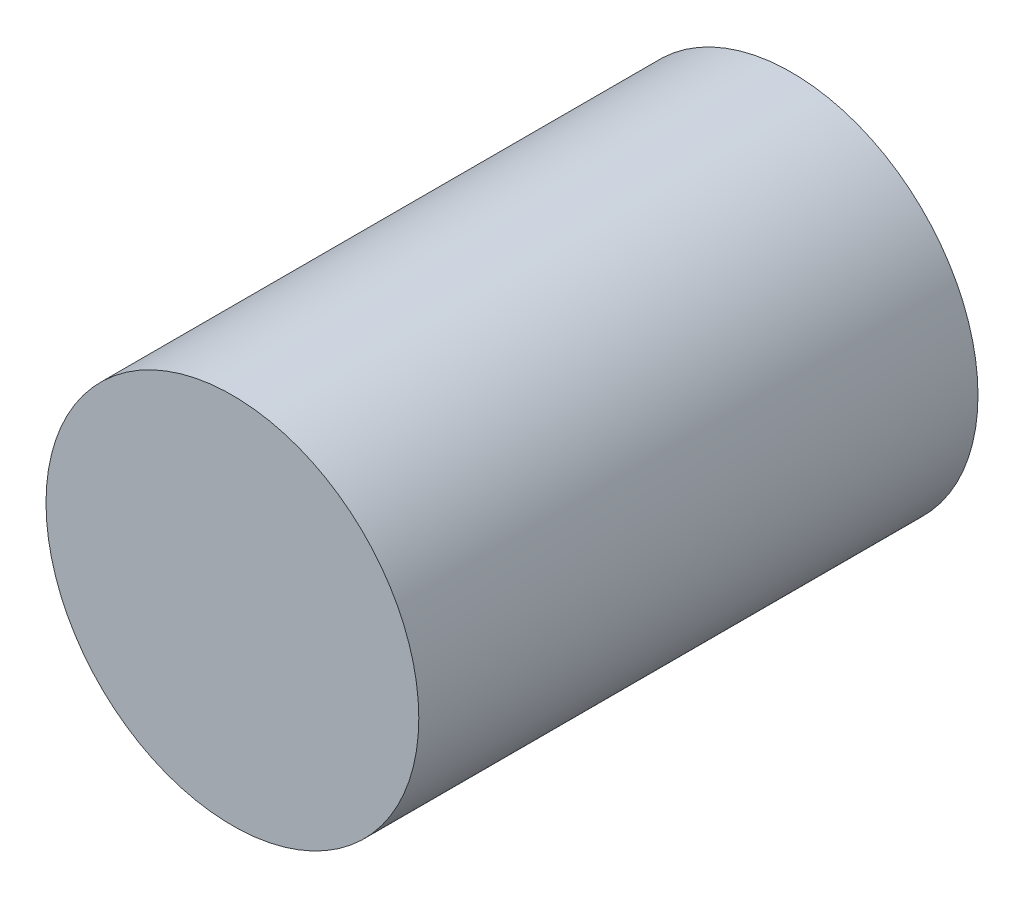
SolidWorks part; units mm, degrees
ref_plane "Front Plane" through (0, 0, 0) normal (0, 0, 1) x (1, 0, 0)
ref_plane "Top Plane" through (0, 0, 0) normal (0, 1, 0) x (1, 0, 0)
ref_plane "Right Plane" through (0, 0, 0) normal (1, 0, 0) x (0, 0, -1)
sketch "Sketch1" plane through (0, 0, 0) normal (0, 0, 1) x (1, 0, 0)
  circle A0 centre (0, 0) radius 2
extrude "Boss-Extrude1" add sketch "Sketch1" along normal blind 6
